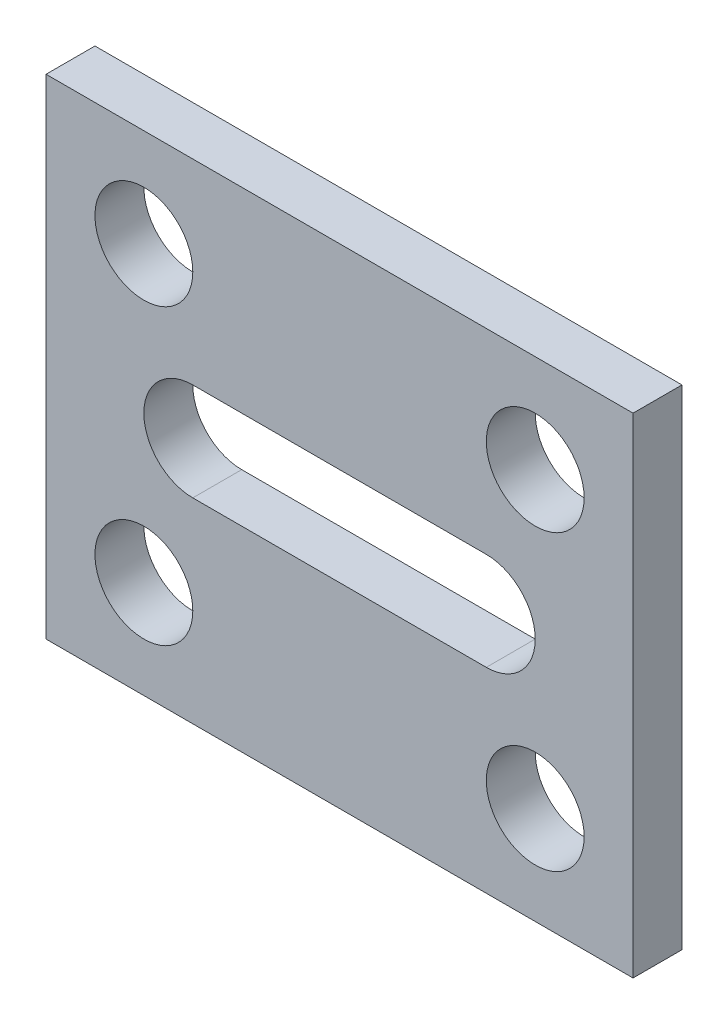
SolidWorks part; units mm, degrees
ref_plane "Front Plane" through (0, 0, 0) normal (0, 0, 1) x (1, 0, 0)
ref_plane "Top Plane" through (0, 0, 0) normal (0, 1, 0) x (1, 0, 0)
ref_plane "Right Plane" through (0, 0, 0) normal (1, 0, 0) x (0, 0, -1)
sketch "Sketch1" plane through (0, 0, 0) normal (0, 0, 1) x (1, 0, 0)
  line L0 (60, 100) -> (60, 0) construction
  line L1 (0, 0) -> (120, 0)
  line L2 (0, 0) -> (0, 100)
  line L3 (0, 100) -> (120, 100)
  line L4 (120, 0) -> (120, 100)
  line L5 (30, 50) -> (90, 50) construction
  line L6 (30, 60) -> (90, 60)
  line L7 (30, 40) -> (90, 40)
  circle A0 centre (20, 80) radius 10
  circle A1 centre (100, 80) radius 10
  circle A2 centre (100, 20) radius 10
  circle A3 centre (20, 20) radius 10
  arc A4 (30, 60) -> (30, 40) centre (30, 50) ccw
  arc A5 (90, 40) -> (90, 60) centre (90, 50) ccw
  point P17 (60, 50)
  dimension "D3" = 20
  dimension "D9" = 10
  dimension "D1" = 100
  dimension "D2" = 120
  dimension "D4" = 20
  dimension "D5" = 20
  dimension "D8" = 60
  dimension "D6" = 2
  dimension "D7" = 2
extrude "Boss-Extrude1" add sketch "Sketch1" along normal blind 10
